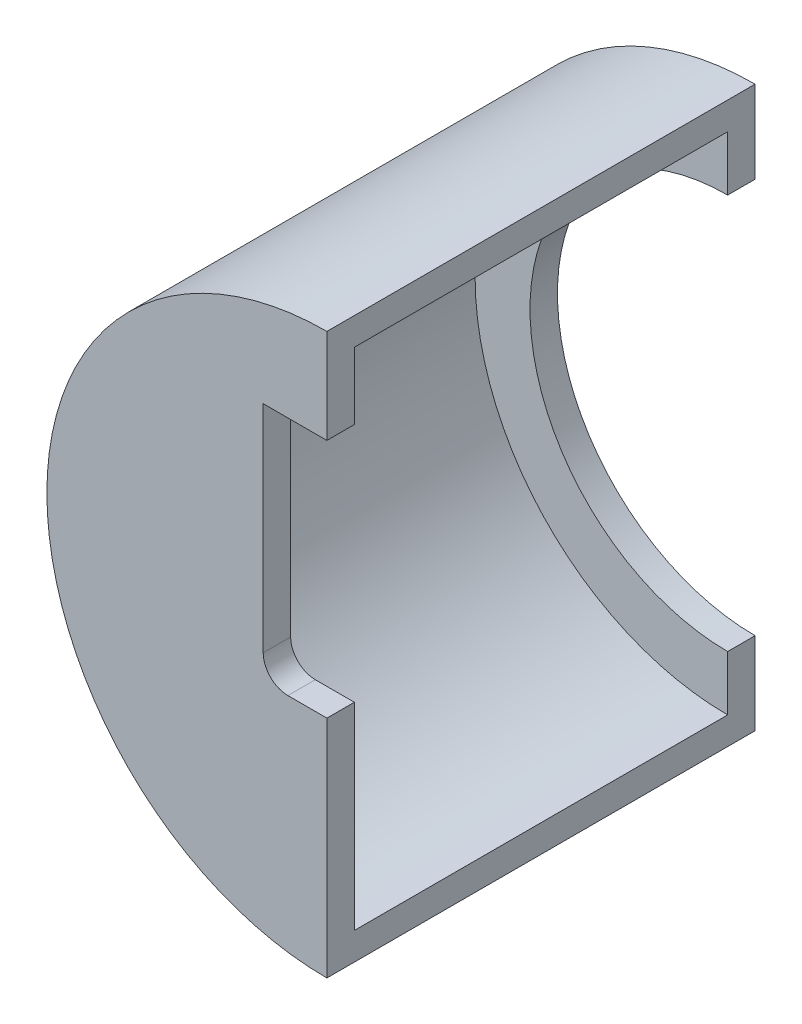
SolidWorks part; units mm, degrees
ref_plane "Plan de face" through (0, 0, 0) normal (0, 0, 1) x (1, 0, 0)
ref_plane "Plan de dessus" through (0, 0, 0) normal (0, 1, 0) x (1, 0, 0)
ref_plane "Plan de droite" through (0, 0, 0) normal (1, 0, 0) x (0, 0, -1)
sketch "Esquisse1" plane through (0, 0, 0) normal (0, 0, 1) x (1, 0, 0)
  line L0 (0, 54.1543) -> (0, -54.1543) construction
  line L1 (-103.4367, 0) -> (52.1834, 0) construction
  line L2 (0, 51) -> (0, 46)
  line L3 (0, -46) -> (0, -51)
  arc A0 (0, 46) -> (0, -46) centre (0, 0) ccw
  arc A1 (0, 51) -> (0, -51) centre (0, 0) ccw
  dimension "D1" = 46
  dimension "D2" = 5
extrude "Boss.-Extru.1" add sketch "Esquisse1" along normal mid plane 68
sketch "Esquisse2" plane through (0, 0, 34) normal (0, 0, 1) x (1, 0, 0)
  line L0 (0, 51) -> (0, -51)
  arc A0 (0, 51) -> (0, -51) centre (0, 0) ccw
  arc A1 (0, 51) -> (0, -51) centre (0, 0) ccw construction
extrude "Boss.-Extru.2" add sketch "Esquisse2" along normal blind 5
sketch "Esquisse3" plane through (0, 0, -34) normal (0, 0, -1) x (-1, 0, 0)
  line L0 (0, 51) -> (0, 36)
  line L1 (0, -51) -> (0, -36)
  arc A0 (0, -51) -> (0, 51) centre (0, 0) ccw
  arc A1 (0, -51) -> (0, 51) centre (0, 0) ccw construction
  arc A2 (0, -36) -> (0, 36) centre (0, 0) ccw
  arc A3 (0, -46) -> (0, 46) centre (0, 0) ccw construction
  dimension "D1" = 10
extrude "Boss.-Extru.3" add sketch "Esquisse3" along normal blind 5
sketch "Esquisse4" plane through (0, 0, 39) normal (0, 0, 1) x (1, 0, 0)
  line L0 (-35.4912, 0) -> (41.3624, 0) construction
  line L1 (-11.6, -2) -> (11.6, -2)
  line L2 (-11.6, -2) -> (-11.6, -33.8)
  line L3 (-11.6, -33.8) -> (11.6, -33.8)
  line L4 (11.6, -2) -> (11.6, -33.8)
  line L5 (-11.6, -2) -> (-11.6, 5.5)
  line L6 (11.6, -2) -> (11.6, 5.5)
  line L7 (-7.1, 10) -> (7.1, 10)
  line L8 (-7.1, -10) -> (7.1, -10)
  line L9 (11.6, 2) -> (11.6, -5.5)
  line L10 (-11.6, 2) -> (-11.6, -5.5)
  line L11 (11.6, 2) -> (11.6, 33.8)
  line L12 (-11.6, 33.8) -> (11.6, 33.8)
  line L13 (-11.6, 2) -> (-11.6, 33.8)
  line L14 (-11.6, 2) -> (11.6, 2)
  arc A0 (-11.6, 5.5) -> (-7.1, 10) centre (-7.1, 5.5) cw
  arc A1 (7.1, 10) -> (11.6, 5.5) centre (7.1, 5.5) cw
  circle A2 centre (0, 0) radius 2.15
  circle A3 centre (0, 0) radius 2.15
  arc A4 (7.1, -10) -> (11.6, -5.5) centre (7.1, -5.5) ccw
  arc A5 (-11.6, -5.5) -> (-7.1, -10) centre (-7.1, -5.5) ccw
  line M18 (0, -51) -> (0, 51)
  dimension "D3" = 4.3
  dimension "D6" = 4.5
  dimension "D7" = 4.5
  dimension "D1" = 2
  dimension "D2" = 11.6
  dimension "D4" = 43.8
  dimension "D5" = 23.2
  dimension "D8" = 12
extrude "Enlèv. mat.-Extru.1" cut sketch "Esquisse4" against normal blind 10 contours L13 A0 L7 L12 M18 | A2 L7 A0 L5 L14 M18 | L10 L0 A2 L14 | L0 L5 L1 A3 | L2 A5 L8 A2 L1 M18 | L0 A3 L1 M18 | A2 L0 L14 M18
